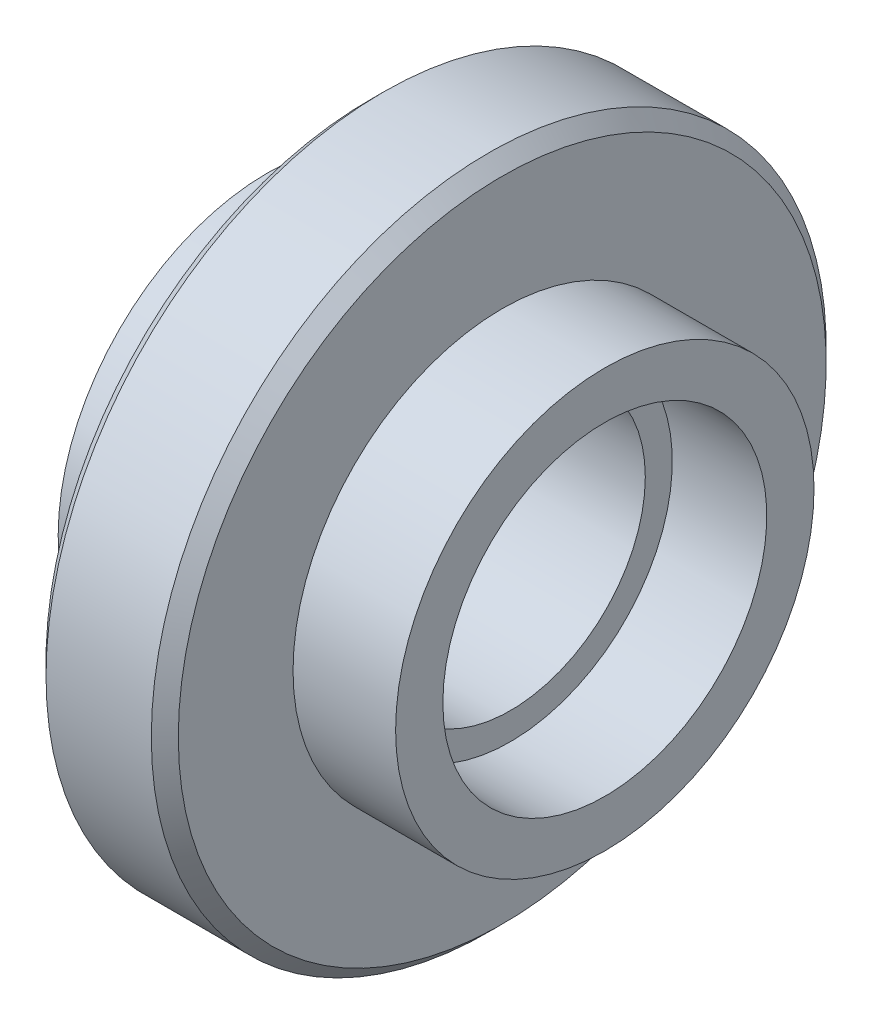
SolidWorks part; units mm, degrees
material "PA Тип 6"
ref_plane "Спереди" through (0, 0, 0) normal (0, 0, 1) x (1, 0, 0)
ref_plane "Сверху" through (0, 0, 0) normal (0, 1, 0) x (1, 0, 0)
ref_plane "Справа" through (0, 0, 0) normal (1, 0, 0) x (0, 0, -1)
sketch "Эскиз1" plane through (0, 0, 0) normal (0, 0, 1) x (1, 0, 0)
  line L0 (0, 0) -> (0, 25) construction
  line L1 (-5.5, 10) -> (5.5, 10)
  line L2 (5.5, 10) -> (5.5, 12)
  line L3 (5.5, 12) -> (12.5, 12)
  line L4 (12.5, 12) -> (12.5, 15.5)
  line L5 (12.5, 15.5) -> (4.9, 15.5)
  line L6 (4.9, 15.5) -> (4.9, 25)
  line L7 (-24.6188, 0) -> (34.4827, 0) construction
  line L8 (-4.9, 15.5) -> (-4.9, 25)
  line L9 (-12.5, 15.5) -> (-4.9, 15.5)
  line L10 (-12.5, 12) -> (-12.5, 15.5)
  line L11 (-5.5, 12) -> (-12.5, 12)
  line L12 (-5.5, 10) -> (-5.5, 12)
  line L13 (-4.9, 25) -> (4.9, 25)
  point P20 (0, 10)
  dimension "D8" = 9.5
  dimension "D1" = 12.5
  dimension "D2" = 9.8
  dimension "D3" = 7
  dimension "D4" = 10
  dimension "D5" = 12
  dimension "D6" = 3.5
  dimension "D7" = 25
  dimension "D9" = 7.6
revolve "Повернуть1" add sketch "Эскиз1" angle 360 about L7
chamfer "Фаска1" distance 1 angle 45 2 edges at (-4.9, 0, 25) (4.9, 0, 25)
